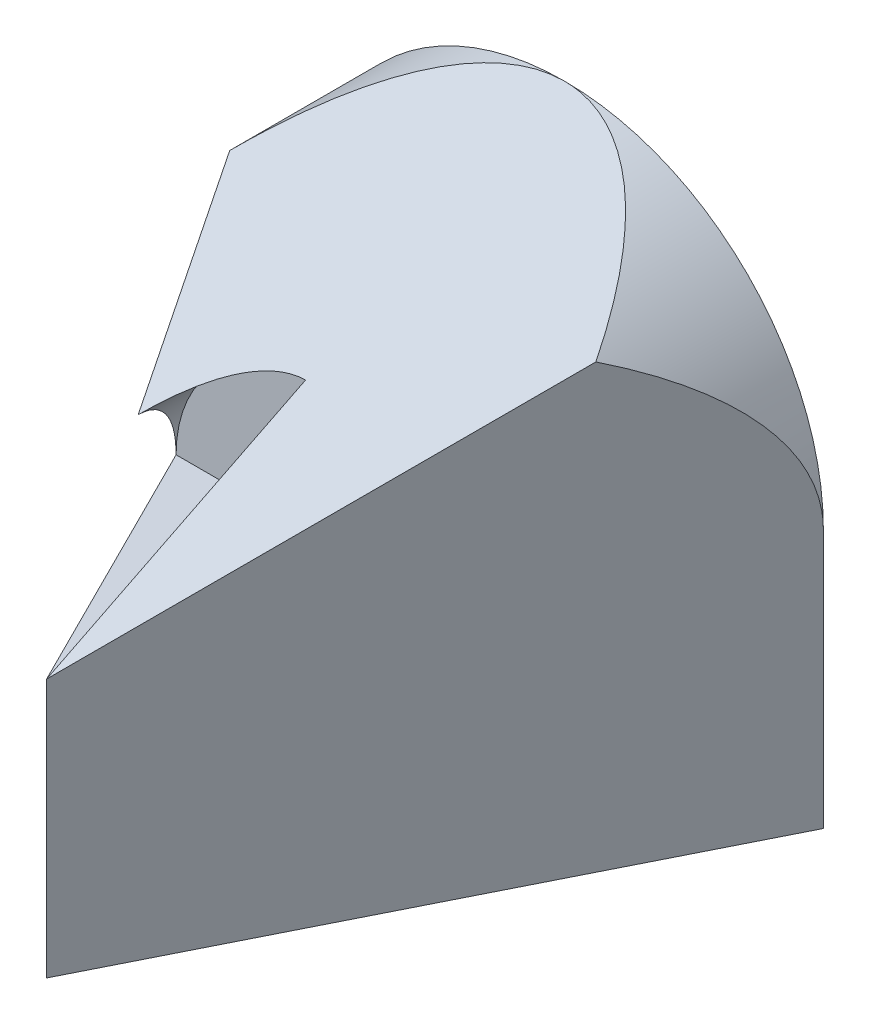
SolidWorks part; units mm, degrees
ref_plane "Front Plane" through (0, 0, 0) normal (0, 0, 1) x (1, 0, 0)
ref_plane "Top Plane" through (0, 0, 0) normal (0, 1, 0) x (1, 0, 0)
ref_plane "Right Plane" through (0, 0, 0) normal (1, 0, 0) x (0, 0, -1)
sketch "Sketch1" plane through (0, 0, 0) normal (0, 0, 1) x (1, 0, 0)
  line L1 (0, 0) -> (40, 0)
  line L2 (0, 0) -> (0, 20)
  line L3 (0, 20) -> (40, 20)
  line L4 (40, 0) -> (40, 20)
  arc A0 (40, 20) -> (0, 20) centre (20, 20) ccw
  dimension "D1" = 40
  dimension "D2" = 20
extrude "Boss-Extrude1" add sketch "Sketch1" along normal blind 40 contours L3 A0 | L1 L4 L3 L2
sketch "Sketch4" plane through (0, 0, 40) normal (0, 0, 1) x (1, 0, 0)
  line L0 (20, 30) -> (20, 20)
  line L1 (20, 20) -> (10, 20)
  arc A0 (20, 30) -> (10, 20) centre (20, 20) ccw
  dimension "D1" = 10
  dimension "D2" = 10
  dimension "D3" = 0
extrude "Cut-Extrude18" cut sketch "Sketch4" against normal blind 20
sketch "Sketch11" plane through (0, 0, 0) normal (0, 1, 0) x (1, 0, 0)
  line L0 (0, 0) -> (20, -40)
  line L1 (20, -40) -> (40, 0)
  line L2 (40, 0) -> (40, -40)
  line L3 (40, -40) -> (0, -40)
  line L4 (0, -40) -> (0, 0)
extrude "Cut-Extrude20" cut sketch "Sketch11" along normal blind 59 contours L4 L3 L0 | L3 L2 L1
sketch "Sketch12" plane through (0, 0, 0) normal (1, 0, 0) x (0, 0, -1)
  line L0 (-40, 20) -> (0, 40)
  line L1 (0, 40) -> (-40, 40)
  line L2 (-40, 40) -> (-40, 20)
extrude "Cut-Extrude21" cut sketch "Sketch12" along normal blind 59
